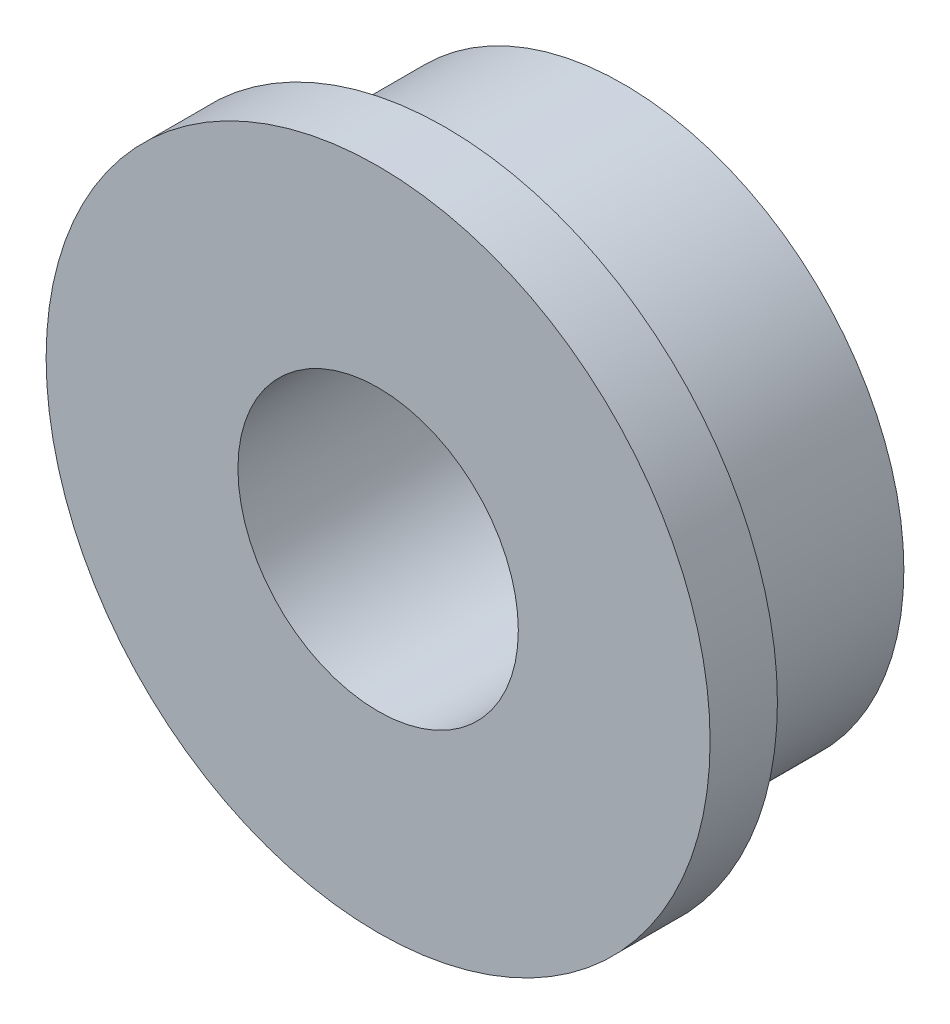
SolidWorks part; units mm, degrees
material "AISI 316 Stainless Steel Sheet (SS)"
ref_plane "Front Plane" through (0, 0, 0) normal (0, 0, 1) x (1, 0, 0)
ref_plane "Top Plane" through (0, 0, 0) normal (0, 1, 0) x (1, 0, 0)
ref_plane "Right Plane" through (0, 0, 0) normal (1, 0, 0) x (0, 0, -1)
sketch "Sketch1" plane through (0, 0, 0) normal (0, 0, 1) x (1, 0, 0)
  circle A0 centre (0, 0) radius 3.175
  circle A1 centre (0, 0) radius 1.5875
  dimension "D1" = 3.175
  dimension "D2" = 6.35
extrude "Boss-Extrude1" add sketch "Sketch1" along normal blind 2.0161
sketch "Sketch2" plane through (0, 0, 2.0161) normal (0, 0, 1) x (1, 0, 0)
  circle A0 centre (0, 0) radius 3.7592
  circle A1 centre (0, 0) radius 1.5875
  circle A2 centre (0, 0) radius 1.5875 construction
  dimension "D1" = 7.5184
extrude "Boss-Extrude2" add sketch "Sketch2" along normal blind 0.762
